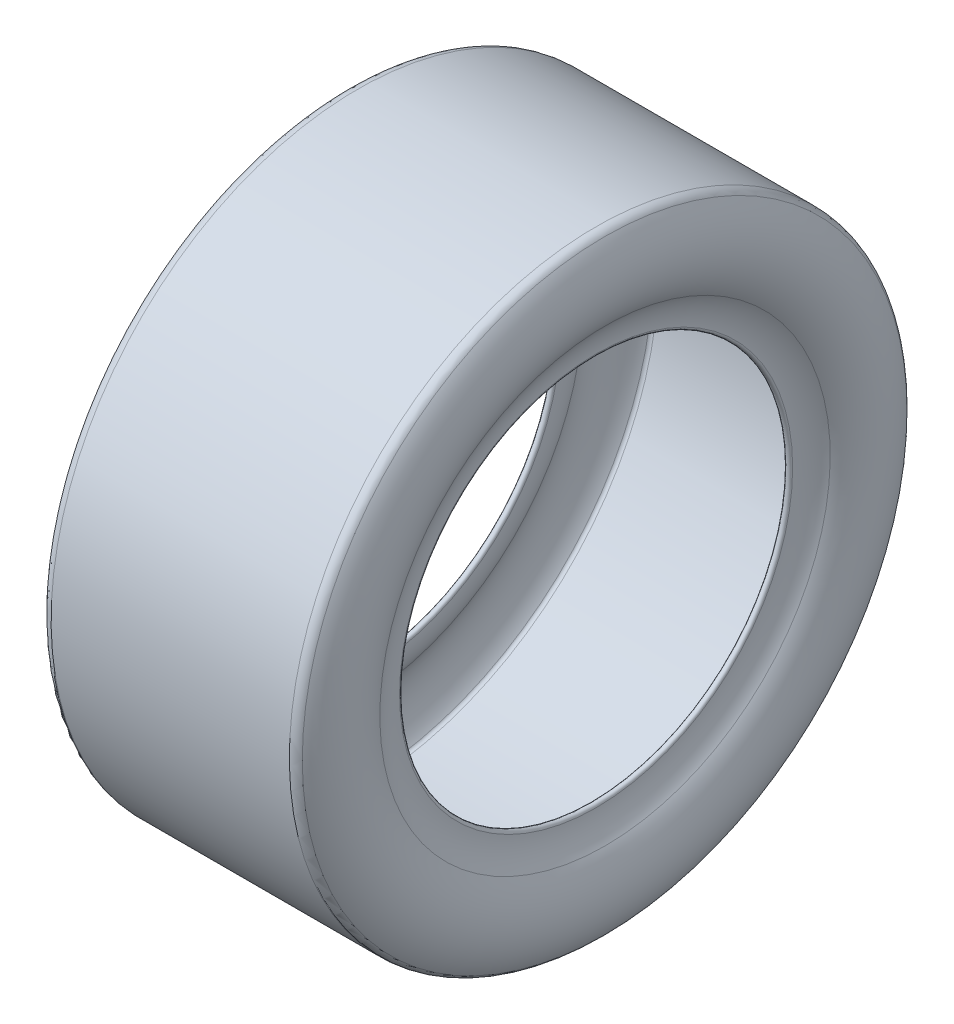
SolidWorks part; units mm, degrees
material "Rubber"
ref_plane "Front Plane" through (0, 0, 0) normal (0, 0, 1) x (1, 0, 0)
ref_plane "Top Plane" through (0, 0, 0) normal (0, 1, 0) x (1, 0, 0)
ref_plane "Right Plane" through (0, 0, 0) normal (1, 0, 0) x (0, 0, -1)
sketch "Sketch3" plane through (0, 0, 0) normal (0, 0, 1) x (1, 0, 0)
  line L0 (-101.6, 261.62) -> (101.6, 261.62)
  line L1 (0, -55) -> (0, 55) construction
  line L2 (-101.6, 256.54) -> (101.6, 256.54)
  line L3 (-23.1787, 0) -> (23.1787, 0) construction
  line L4 (55, 0) -> (-55, 0) construction
  line L5 (0, 261.62) -> (0, 0) construction
  arc A0 (-101.6, 261.62) -> (-108.8602, 257.858) centre (-101.6, 252.7335) ccw
  arc A1 (-96.52, 167.64) -> (-105.0281, 194.9498) centre (-144.6044, 167.64) ccw
  arc A2 (-105.0281, 194.9498) -> (-104.7099, 254.9285) centre (-61.8993, 224.7112) cw
  arc A3 (-108.8602, 257.858) -> (-109.2093, 192.0646) centre (-61.8993, 224.7112) ccw
  arc A4 (-109.2093, 192.0646) -> (-101.6, 167.64) centre (-144.6044, 167.64) cw
  arc A5 (-101.6, 167.64) -> (-96.52, 167.64) centre (-99.06, 167.64) ccw
  arc A6 (-104.7099, 254.9285) -> (-101.6, 256.54) centre (-101.6, 252.7335) cw
  arc A7 (101.6, 167.64) -> (96.52, 167.64) centre (99.06, 167.64) cw
  arc A8 (96.52, 167.64) -> (105.0281, 194.9498) centre (144.6044, 167.64) cw
  arc A9 (109.2093, 192.0646) -> (101.6, 167.64) centre (144.6044, 167.64) ccw
  arc A10 (105.0281, 194.9498) -> (104.7099, 254.9285) centre (61.8993, 224.7112) ccw
  arc A11 (108.8602, 257.858) -> (109.2093, 192.0646) centre (61.8993, 224.7112) cw
  arc A12 (104.7099, 254.9285) -> (101.6, 256.54) centre (101.6, 252.7335) ccw
  arc A13 (101.6, 261.62) -> (108.8602, 257.858) centre (101.6, 252.7335) cw
  point P2 (0, 261.62)
  dimension "D3" = 119.38
  dimension "D4" = 2.54
  dimension "D5" = 165.1
  dimension "D1" = 203.2
  dimension "D2" = 261.62
  dimension "D6" = 101.6
revolve "Tire" add sketch "Sketch3" angle 360 about L3
sketch "Tire Patch Locater" plane through (0, 0, 0) normal (1, 0, 0) x (0, 0, -1)
  circle A0 centre (0, 0) radius 261.62 construction
